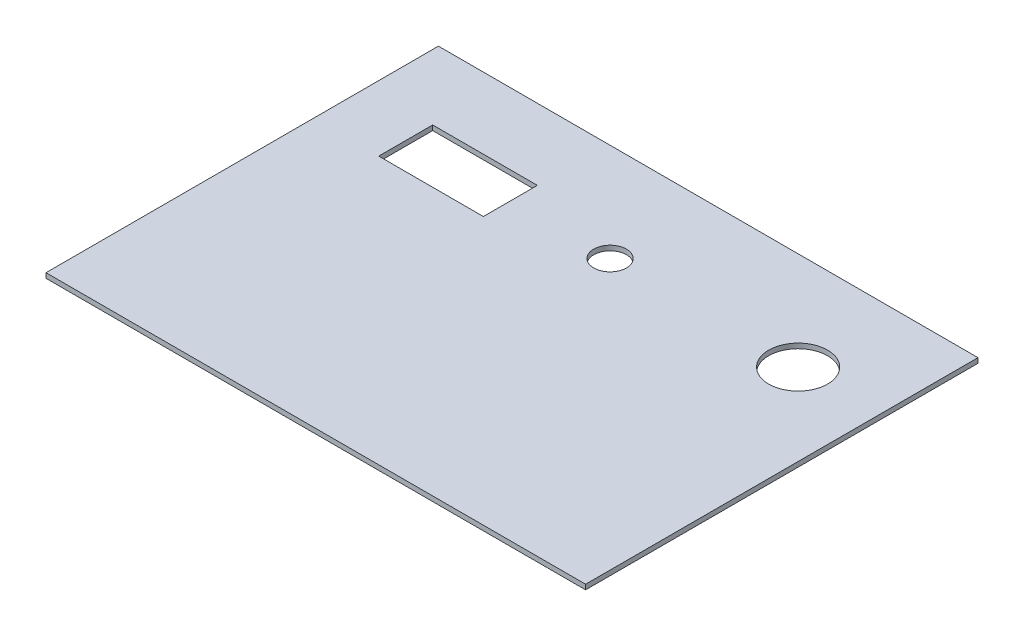
SolidWorks part; units mm, degrees
ref_plane "Ön Düzlem" through (0, 0, 0) normal (0, 0, 1) x (1, 0, 0)
ref_plane "Üst Düzlem" through (0, 0, 0) normal (0, 1, 0) x (1, 0, 0)
ref_plane "Sağ Düzlem" through (0, 0, 0) normal (1, 0, 0) x (0, 0, -1)
sketch "Çizim1" plane through (0, 0, 0) normal (0, 1, 0) x (1, 0, 0)
  line L1 (0, 0) -> (330, 0)
  line L2 (0, 0) -> (0, -240)
  line L3 (0, -240) -> (330, -240)
  line L4 (330, 0) -> (330, -240)
  line L5 (40, -43.5) -> (104, -43.5)
  line L6 (40, -43.5) -> (40, -76.5)
  line L7 (40, -76.5) -> (104, -76.5)
  line L8 (104, -43.5) -> (104, -76.5)
  circle A0 centre (280, -60) radius 18
  circle A1 centre (165, -60) radius 10
  point P13 (165, 0)
  point P14 (0, 0)
  point P15 (104, -60)
  dimension "D3" = 36
  dimension "D5" = 50
  dimension "D10" = 20
  dimension "D1" = 330
  dimension "D2" = 240
  dimension "D4" = 60
  dimension "D6" = 64
  dimension "D7" = 33
  dimension "D9" = 40
extrude "Yükseklik-Ekstrüzyon1" add sketch "Çizim1" along normal blind 3
